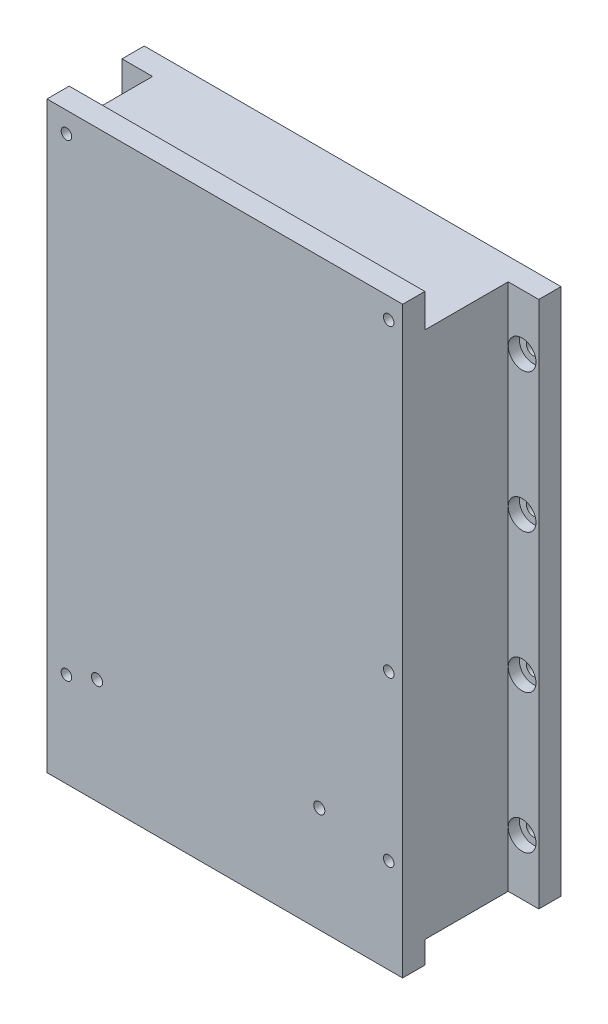
SolidWorks part; units mm, degrees
material "PLA_printed_black"
ref_plane "Front Plane" through (0, 0, 0) normal (0, 0, 1) x (1, 0, 0)
ref_plane "Top Plane" through (0, 0, 0) normal (0, 1, 0) x (1, 0, 0)
ref_plane "Right Plane" through (0, 0, 0) normal (1, 0, 0) x (0, 0, -1)
sketch "Sketch1" plane through (0, 0, 0) normal (0, 0, 1) x (1, 0, 0)
  line L1 (0, 0) -> (75, 0)
  line L2 (0, 0) -> (0, 95)
  line L3 (0, 95) -> (75, 95)
  line L4 (75, 0) -> (75, 95)
  dimension "D1" = 75
  dimension "D2" = 95
extrude "Boss-Extrude1" add sketch "Sketch1" along normal blind 23
sketch "Sketch2" plane through (0, 0, 0) normal (0, 0, 1) x (1, 0, 0)
  line L0 (0, 0) -> (75, 0) construction
  line L1 (0, 95) -> (6, 95)
  line L2 (0, 95) -> (0, 0)
  line L3 (0, 0) -> (6, 0)
  line L4 (6, 95) -> (6, 0)
  line L6 (75, 95) -> (69, 95)
  line L7 (75, 95) -> (75, 0)
  line L8 (75, 0) -> (69, 0)
  line L9 (69, 95) -> (69, 0)
  dimension "D1" = 6
  dimension "D2" = 6
  dimension "D3" = 95
extrude "Cut-Extrude1" [suppressed] cut sketch "Sketch2" against normal offset from surface (20 mm away) 3
sketch "Sketch3" plane through (0, 0, 0) normal (0, 0, -1) x (-1, 0, 0)
  line L1 (-65, 90) -> (-10, 90)
  line L2 (-65, 90) -> (-65, 5)
  line L3 (-65, 5) -> (-10, 5)
  line L4 (-10, 90) -> (-10, 5)
  line L6 (-75, 0) -> (-75, 95) construction
  line L7 (0, 95) -> (0, 0) construction
  line L9 (-75, 95) -> (0, 95) construction
  dimension "D1" = 10
  dimension "D2" = 10
  dimension "D3" = 85
  dimension "D4" = 5
extrude "Cut-Extrude2" cut sketch "Sketch3" against normal offset from surface (19 mm away) 4
ref_plane "Plane1" through (0, 0, 19) normal (0, 0, -1) x (-1, 0, 0)
sketch "Sketch11" plane through (0, 0, 19) normal (0, 0, -1) x (-1, 0, 0)
  line L0 (-75, 95) -> (0, 95) construction
  line L1 (-5.5, 101) -> (-69.5, 101)
  line L3 (-5.5, -4) -> (-69.5, -4)
  line L5 (0, 0) -> (-75, 0) construction
  line L6 (-5.5, 101) -> (-5.5, -4)
  line L7 (-69.5, 101) -> (-69.5, -4)
  line L8 (0, 95) -> (0, 0) construction
  line L9 (-75, 0) -> (-75, 95) construction
  point P6 (-37.5, 95)
  dimension "D1" = 6
  dimension "D2" = 4
  dimension "D3" = 5.5
  dimension "D4" = 5.5
extrude "Boss-Extrude2" add sketch "Sketch11" against normal blind 4
sketch "Sketch5" plane through (0, 0, 23) normal (0, 0, 1) x (1, 0, 0)
  line L0 (75, 95) -> (69.5, 95) construction
  line L1 (75, 0) -> (69.5, 0)
  line L2 (75, 0) -> (75, 95)
  line L3 (75, 95) -> (69.5, 95)
  line L4 (69.5, 0) -> (69.5, 95)
  line L5 (0, 0) -> (5.5, 0) construction
  line L6 (0, 95) -> (5.5, 95)
  line L7 (0, 95) -> (0, 0)
  line L8 (0, 0) -> (5.5, 0)
  line L9 (5.5, 95) -> (5.5, 0)
  dimension "D1" = 5.5
  dimension "D2" = 5.5
extrude "Cut-Extrude4" cut sketch "Sketch5" against normal offset from surface (19 mm away) 4
sketch "Sketch4" plane through (0, 0, 23) normal (0, 0, -1) x (-1, 0, 0)
  line L0 (-65, 0) -> (-10, 0) construction
  line L1 (-65, 95) -> (-10, 95) construction
  line L3 (-10, 90) -> (-10, 5) construction
  line L4 (-5.5, 101) -> (-69.5, 101) construction
  circle A0 centre (-9, 97.31) radius 0.95
  circle A1 centre (-67, 97.31) radius 0.95
  circle A2 centre (-67, 42.51) radius 0.95
  circle A3 centre (-67, 13.01) radius 0.95
  circle A4 centre (-9, 13.01) radius 0.95
  circle A5 centre (-14.5, 15) radius 1
  circle A6 centre (-54.5, 15) radius 1
  point P0 (-37.5, 0)
  point P1 (-37.5, 95)
  point P4 (-34.5, 15)
  dimension "D6" = 1.9
  dimension "D7" = 2
  dimension "D1" = 82.31
  dimension "D2" = 58
  dimension "D3" = 40
  dimension "D4" = 5.5
  dimension "D5" = 84.3
  dimension "D8" = 20
  dimension "D9" = 1
  dimension "D10" = 54.8
  dimension "D11" = 3.69
extrude "Cut-Extrude3" cut sketch "Sketch4" along normal blind 10
sketch "Sketch6" plane through (0, 0, 4) normal (0, 0, 1) x (1, 0, 0)
  line L0 (75, 0) -> (75, 95) construction
  line L1 (0, 95) -> (0, 0) construction
  line L2 (69.5, 0) -> (75, 0) construction
  circle A0 centre (72, 10) radius 1.25
  circle A1 centre (3, 10) radius 1.25
  circle A2 centre (72, 35) radius 1.25
  circle A3 centre (3, 35) radius 1.25
  circle A4 centre (72, 60) radius 1.25
  circle A5 centre (3, 60) radius 1.25
  circle A6 centre (72, 85) radius 1.25
  circle A7 centre (3, 85) radius 1.25
  dimension "D1" = 3
  dimension "D3" = 2.5
  dimension "D5" = 69
  dimension "D2" = 3
  dimension "D6" = 10
  dimension "D4" = 4
extrude "Cut-Extrude5" cut sketch "Sketch6" against normal through all
sketch "Sketch7" plane through (0, 5, 0) normal (0, 1, 0) x (1, 0, 0)
  line L0 (10, -19) -> (65, -19) construction
  line L1 (10, -19) -> (60, -19)
  line L2 (10, -19) -> (10, -11)
  line L3 (10, -11) -> (60, -11)
  line L4 (60, -19) -> (60, -11)
  line L6 (10, -19) -> (10, 0) construction
  dimension "D1" = 50
  dimension "D2" = 0
  dimension "D3" = 8
extrude "Cut-Extrude6" cut sketch "Sketch7" against normal up to next
sketch "Sketch10" plane through (0, 0, 4) normal (0, 0, 1) x (1, 0, 0)
  circle A0 centre (72, 10) radius 2.5
  circle A1 centre (72, 35) radius 2.5
  circle A2 centre (72, 60) radius 2.5
  circle A3 centre (72, 85) radius 2.5
  circle A4 centre (3, 10) radius 2.5
  circle A5 centre (3, 35) radius 2.5
  circle A6 centre (3, 60) radius 2.5
  circle A7 centre (3, 85) radius 2.5
  dimension "D1" = 5
extrude "Cut-Extrude9" cut sketch "Sketch10" against normal blind 2
